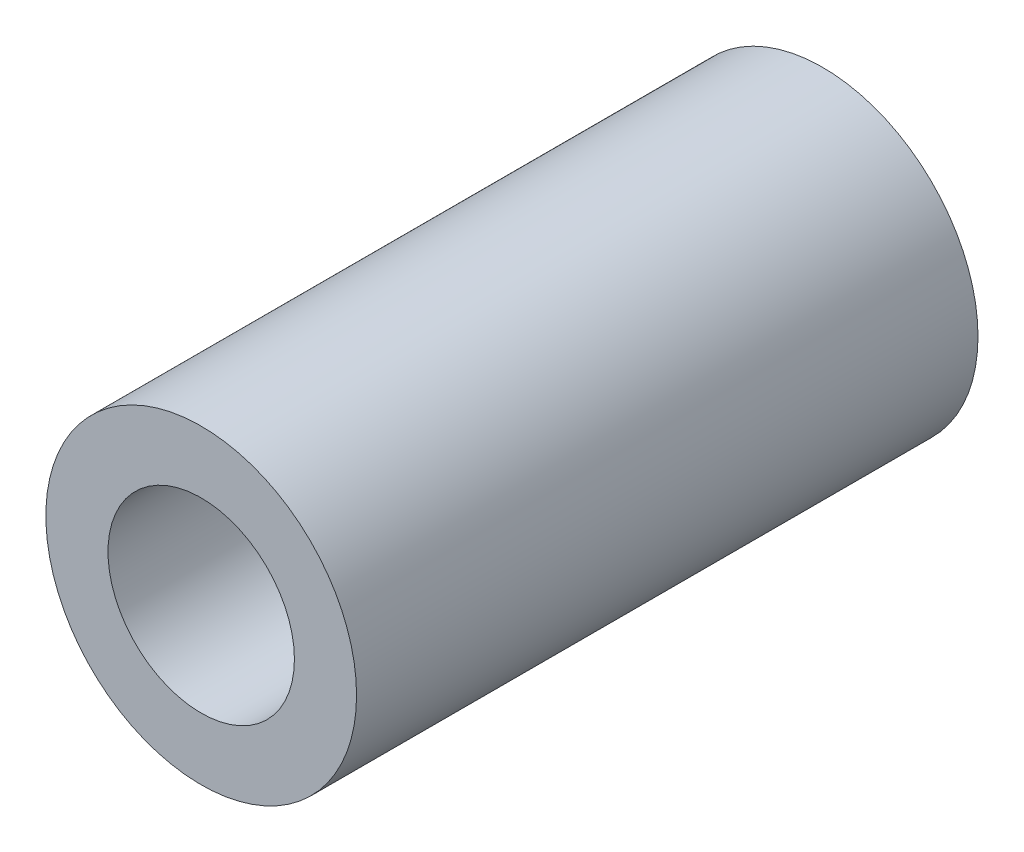
SolidWorks part; units mm, degrees
ref_plane "Plan de face" through (0, 0, 0) normal (0, 0, 1) x (1, 0, 0)
ref_plane "Plan de dessus" through (0, 0, 0) normal (0, 1, 0) x (1, 0, 0)
ref_plane "Plan de droite" through (0, 0, 0) normal (1, 0, 0) x (0, 0, -1)
sketch "Esquisse1" plane through (0, 0, 0) normal (0, 0, 1) x (1, 0, 0)
  circle A0 centre (0, 0) radius 5
  circle A1 centre (0, 0) radius 3
  dimension "D1" = 10
  dimension "D2" = 6
extrude "Boss.-Extru.1" add sketch "Esquisse1" along normal blind 20
